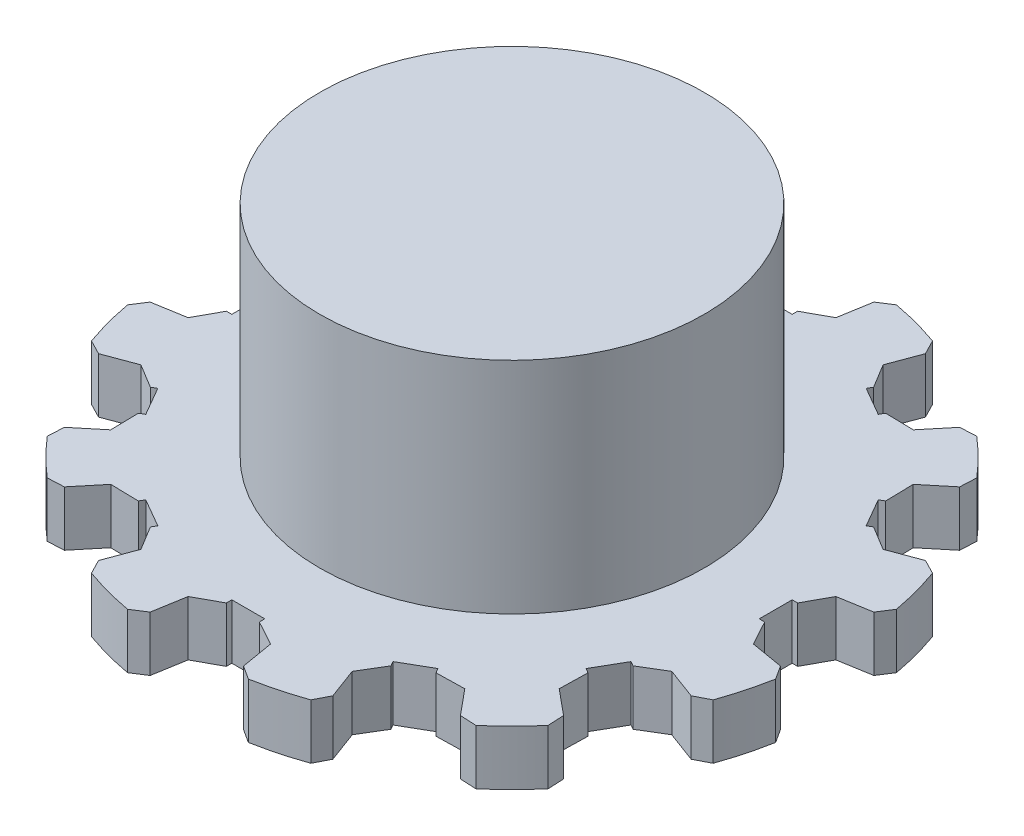
SolidWorks part; units mm, degrees
ref_plane "Front Plane" through (0, 0, 0) normal (0, 0, 1) x (1, 0, 0)
ref_plane "Top Plane" through (0, 0, 0) normal (0, 1, 0) x (1, 0, 0)
ref_plane "Right Plane" through (0, 0, 0) normal (1, 0, 0) x (0, 0, -1)
sketch "Sketch1" plane through (0, 0, 0) normal (0, 1, 0) x (1, 0, 0)
  line L0 (0, -1000) -> (0, 49000) construction
  line L1 (-3.75, 25.7281) -> (-4.25, 28.6869)
  line L2 (3.75, 25.7281) -> (4.25, 28.6869)
  line L3 (-3.75, 25.7281) -> (-1.5, 24.4948)
  line L4 (1.5, 24) -> (-1.5, 24)
  line L8 (-1.5, 24) -> (-1.5, 24.4948)
  line L9 (1.5, 24) -> (1.5, 24.4948)
  line L10 (3.75, 25.7281) -> (1.5, 24.4948)
  line L11 (4.25, 28.6869) -> (5.5, 29.4915)
  line L12 (-4.25, 28.6869) -> (-5.5, 29.4915)
  line L13 (18.0241, 22.7186) -> (19.5089, 22.7904)
  line L14 (16.1117, 20.4062) -> (18.0241, 22.7186)
  line L15 (16.1117, 20.4062) -> (13.5464, 20.4631)
  line L16 (13.299, 20.0346) -> (13.5464, 20.4631)
  line L17 (13.299, 20.0346) -> (10.701, 21.5346)
  line L18 (10.701, 21.5346) -> (10.9484, 21.9631)
  line L19 (9.6165, 24.1562) -> (10.9484, 21.9631)
  line L20 (9.6165, 24.1562) -> (10.6628, 26.9686)
  line L21 (10.6628, 26.9686) -> (9.9826, 28.2904)
  line L22 (26.9686, 10.6628) -> (28.2904, 9.9826)
  line L23 (24.1562, 9.6165) -> (26.9686, 10.6628)
  line L24 (24.1562, 9.6165) -> (21.9631, 10.9484)
  line L25 (21.5346, 10.701) -> (21.9631, 10.9484)
  line L26 (21.5346, 10.701) -> (20.0346, 13.299)
  line L27 (20.0346, 13.299) -> (20.4631, 13.5464)
  line L28 (20.4062, 16.1117) -> (20.4631, 13.5464)
  line L29 (20.4062, 16.1117) -> (22.7186, 18.0241)
  line L30 (22.7186, 18.0241) -> (22.7904, 19.5089)
  line L31 (28.6869, -4.25) -> (29.4915, -5.5)
  line L32 (25.7281, -3.75) -> (28.6869, -4.25)
  line L33 (25.7281, -3.75) -> (24.4948, -1.5)
  line L34 (24, -1.5) -> (24.4948, -1.5)
  line L35 (24, -1.5) -> (24, 1.5)
  line L36 (24, 1.5) -> (24.4948, 1.5)
  line L37 (25.7281, 3.75) -> (24.4948, 1.5)
  line L38 (25.7281, 3.75) -> (28.6869, 4.25)
  line L39 (28.6869, 4.25) -> (29.4915, 5.5)
  line L40 (22.7186, -18.0241) -> (22.7904, -19.5089)
  line L41 (20.4062, -16.1117) -> (22.7186, -18.0241)
  line L42 (20.4062, -16.1117) -> (20.4631, -13.5464)
  line L43 (20.0346, -13.299) -> (20.4631, -13.5464)
  line L44 (20.0346, -13.299) -> (21.5346, -10.701)
  line L45 (21.5346, -10.701) -> (21.9631, -10.9484)
  line L46 (24.1562, -9.6165) -> (21.9631, -10.9484)
  line L47 (24.1562, -9.6165) -> (26.9686, -10.6628)
  line L48 (26.9686, -10.6628) -> (28.2904, -9.9826)
  line L49 (10.6628, -26.9686) -> (9.9826, -28.2904)
  line L50 (9.6165, -24.1562) -> (10.6628, -26.9686)
  line L51 (9.6165, -24.1562) -> (10.9484, -21.9631)
  line L52 (10.701, -21.5346) -> (10.9484, -21.9631)
  line L53 (10.701, -21.5346) -> (13.299, -20.0346)
  line L54 (13.299, -20.0346) -> (13.5464, -20.4631)
  line L55 (16.1117, -20.4062) -> (13.5464, -20.4631)
  line L56 (16.1117, -20.4062) -> (18.0241, -22.7186)
  line L57 (18.0241, -22.7186) -> (19.5089, -22.7904)
  line L58 (-4.25, -28.6869) -> (-5.5, -29.4915)
  line L59 (-3.75, -25.7281) -> (-4.25, -28.6869)
  line L60 (-3.75, -25.7281) -> (-1.5, -24.4948)
  line L61 (-1.5, -24) -> (-1.5, -24.4948)
  line L62 (-1.5, -24) -> (1.5, -24)
  line L63 (1.5, -24) -> (1.5, -24.4948)
  line L64 (3.75, -25.7281) -> (1.5, -24.4948)
  line L65 (3.75, -25.7281) -> (4.25, -28.6869)
  line L66 (4.25, -28.6869) -> (5.5, -29.4915)
  line L67 (-18.0241, -22.7186) -> (-19.5089, -22.7904)
  line L68 (-16.1117, -20.4062) -> (-18.0241, -22.7186)
  line L69 (-16.1117, -20.4062) -> (-13.5464, -20.4631)
  line L70 (-13.299, -20.0346) -> (-13.5464, -20.4631)
  line L71 (-13.299, -20.0346) -> (-10.701, -21.5346)
  line L72 (-10.701, -21.5346) -> (-10.9484, -21.9631)
  line L73 (-9.6165, -24.1562) -> (-10.9484, -21.9631)
  line L74 (-9.6165, -24.1562) -> (-10.6628, -26.9686)
  line L75 (-10.6628, -26.9686) -> (-9.9826, -28.2904)
  line L76 (-26.9686, -10.6628) -> (-28.2904, -9.9826)
  line L77 (-24.1562, -9.6165) -> (-26.9686, -10.6628)
  line L78 (-24.1562, -9.6165) -> (-21.9631, -10.9484)
  line L79 (-21.5346, -10.701) -> (-21.9631, -10.9484)
  line L80 (-21.5346, -10.701) -> (-20.0346, -13.299)
  line L81 (-20.0346, -13.299) -> (-20.4631, -13.5464)
  line L82 (-20.4062, -16.1117) -> (-20.4631, -13.5464)
  line L83 (-20.4062, -16.1117) -> (-22.7186, -18.0241)
  line L84 (-22.7186, -18.0241) -> (-22.7904, -19.5089)
  line L85 (-28.6869, 4.25) -> (-29.4915, 5.5)
  line L86 (-25.7281, 3.75) -> (-28.6869, 4.25)
  line L87 (-25.7281, 3.75) -> (-24.4948, 1.5)
  line L88 (-24, 1.5) -> (-24.4948, 1.5)
  line L89 (-24, 1.5) -> (-24, -1.5)
  line L90 (-24, -1.5) -> (-24.4948, -1.5)
  line L91 (-25.7281, -3.75) -> (-24.4948, -1.5)
  line L92 (-25.7281, -3.75) -> (-28.6869, -4.25)
  line L93 (-28.6869, -4.25) -> (-29.4915, -5.5)
  line L94 (-22.7186, 18.0241) -> (-22.7904, 19.5089)
  line L95 (-20.4062, 16.1117) -> (-22.7186, 18.0241)
  line L96 (-20.4062, 16.1117) -> (-20.4631, 13.5464)
  line L97 (-20.0346, 13.299) -> (-20.4631, 13.5464)
  line L98 (-20.0346, 13.299) -> (-21.5346, 10.701)
  line L99 (-21.5346, 10.701) -> (-21.9631, 10.9484)
  line L100 (-24.1562, 9.6165) -> (-21.9631, 10.9484)
  line L101 (-24.1562, 9.6165) -> (-26.9686, 10.6628)
  line L102 (-26.9686, 10.6628) -> (-28.2904, 9.9826)
  line L103 (-10.6628, 26.9686) -> (-9.9826, 28.2904)
  line L104 (-9.6165, 24.1562) -> (-10.6628, 26.9686)
  line L105 (-9.6165, 24.1562) -> (-10.9484, 21.9631)
  line L106 (-10.701, 21.5346) -> (-10.9484, 21.9631)
  line L107 (-10.701, 21.5346) -> (-13.299, 20.0346)
  line L108 (-13.299, 20.0346) -> (-13.5464, 20.4631)
  line L109 (-16.1117, 20.4062) -> (-13.5464, 20.4631)
  line L110 (-16.1117, 20.4062) -> (-18.0241, 22.7186)
  line L111 (-18.0241, 22.7186) -> (-19.5089, 22.7904)
  circle A0 centre (0, 0) radius 25 construction
  circle A1 centre (0, 0) radius 26 construction
  circle A2 centre (0, 0) radius 30 construction
  circle A3 centre (0, 0) radius 29 construction
  arc A4 (5.5, 29.4915) -> (8, 28.9137) centre (0, 0) cw
  arc A5 (-5.5, 29.4915) -> (-8, 28.9137) centre (0, 0) ccw
  arc A6 (19.5089, 22.7904) -> (21.385, 21.04) centre (0, 0) cw
  arc A7 (9.9826, 28.2904) -> (7.5286, 29.04) centre (0, 0) ccw
  arc A8 (28.2904, 9.9826) -> (29.04, 7.5286) centre (0, 0) cw
  arc A9 (22.7904, 19.5089) -> (21.04, 21.385) centre (0, 0) ccw
  arc A10 (29.4915, -5.5) -> (28.9137, -8) centre (0, 0) cw
  arc A11 (29.4915, 5.5) -> (28.9137, 8) centre (0, 0) ccw
  arc A12 (22.7904, -19.5089) -> (21.04, -21.385) centre (0, 0) cw
  arc A13 (28.2904, -9.9826) -> (29.04, -7.5286) centre (0, 0) ccw
  arc A14 (9.9826, -28.2904) -> (7.5286, -29.04) centre (0, 0) cw
  arc A15 (19.5089, -22.7904) -> (21.385, -21.04) centre (0, 0) ccw
  arc A16 (-5.5, -29.4915) -> (-8, -28.9137) centre (0, 0) cw
  arc A17 (5.5, -29.4915) -> (8, -28.9137) centre (0, 0) ccw
  arc A18 (-19.5089, -22.7904) -> (-21.385, -21.04) centre (0, 0) cw
  arc A19 (-9.9826, -28.2904) -> (-7.5286, -29.04) centre (0, 0) ccw
  arc A20 (-28.2904, -9.9826) -> (-29.04, -7.5286) centre (0, 0) cw
  arc A21 (-22.7904, -19.5089) -> (-21.04, -21.385) centre (0, 0) ccw
  arc A22 (-29.4915, 5.5) -> (-28.9137, 8) centre (0, 0) cw
  arc A23 (-29.4915, -5.5) -> (-28.9137, -8) centre (0, 0) ccw
  arc A24 (-22.7904, 19.5089) -> (-21.04, 21.385) centre (0, 0) cw
  arc A25 (-28.2904, 9.9826) -> (-29.04, 7.5286) centre (0, 0) ccw
  arc A26 (-9.9826, 28.2904) -> (-7.5286, 29.04) centre (0, 0) cw
  arc A27 (-19.5089, 22.7904) -> (-21.385, 21.04) centre (0, 0) ccw
  point P12 (0, 25)
  point P156 (0, 0)
  dimension "D1" = 50
  dimension "D2" = 52
  dimension "D3" = 60
  dimension "D4" = 58
  dimension "D5" = 3.75
  dimension "D6" = 4.25
  dimension "D8" = 4.25
  dimension "D10" = 3
  dimension "D7" = 3.75
  dimension "D9" = 25
  dimension "D11" = 1.5
  dimension "D12" = 24
  dimension "D13" = 118.729
  dimension "D14" = 118.729
  dimension "D15" = 5.5
  dimension "D16" = 5.5
  dimension "D17" = 8
  dimension "D18" = 8
  dimension "D19" = 12
extrude "Boss-Extrude1" add sketch "Sketch1" along normal blind 5 contours L111 A27 A24 L94 L95 L96 L97 L98 L99 L100 L101 L102 A25 A22 L85 L86 L87 L88 L89 L90 L91 L92 L93 A23 A20 L76 L77 L78 L79 L80 L81 L82 L83 L84 A21 A18 L67 L68 L69 L70 L71 L72 L73 L74 L75 A19 A16
sketch "Sketch2" plane through (0, 5, 0) normal (0, 1, 0) x (1, 0, 0)
  circle A0 centre (0, 0) radius 17.5
  dimension "D1" = 35
extrude "Boss-Extrude3" add sketch "Sketch2" along normal blind 20
